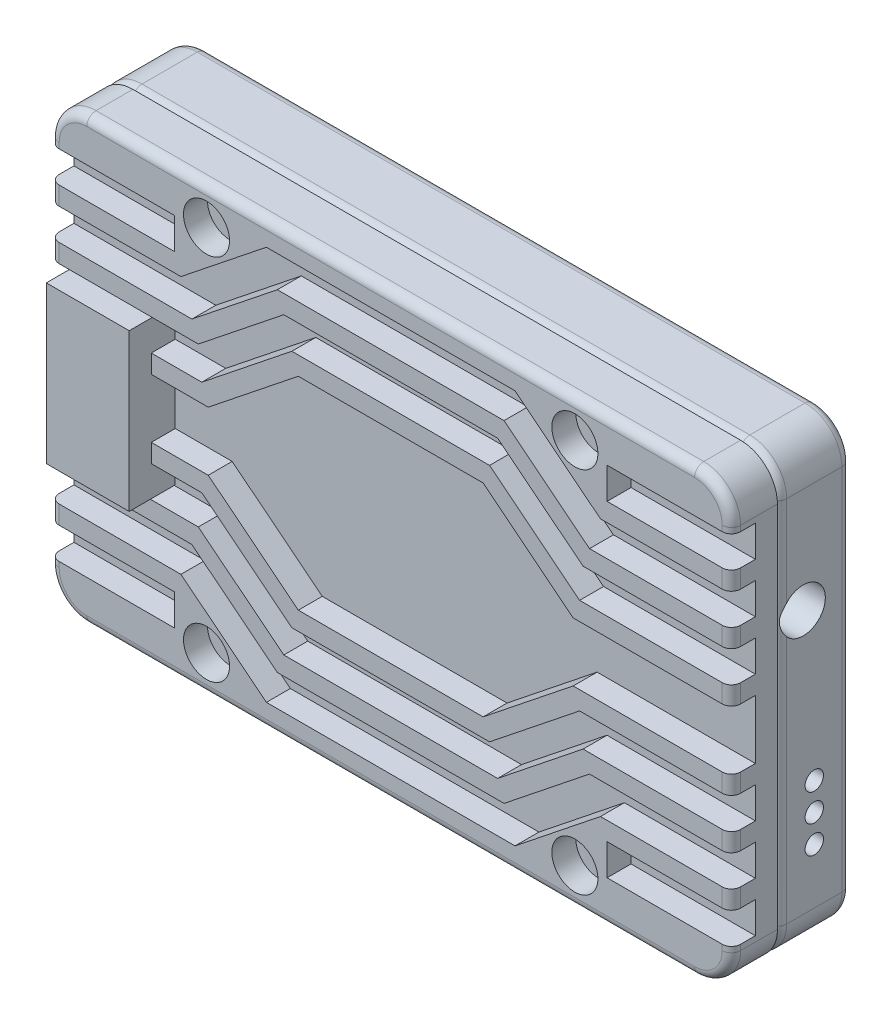
SolidWorks part; units mm, degrees
other "bottom"
other "fin"
other "plug"
ref_plane "Front Plane" through (0, 0, 0) normal (0, 0, 1) x (1, 0, 0)
ref_plane "Top Plane" through (0, 0, 0) normal (0, 1, 0) x (1, 0, 0)
ref_plane "Right Plane" through (0, 0, 0) normal (1, 0, 0) x (0, 0, -1)
sketch "Sketch1" plane through (0, 0, 0) normal (0, 0, 1) x (1, 0, 0)
  line L1 (-16.5, 12) -> (16.5, 12)
  line L2 (-18.5, 10) -> (-18.5, -10)
  line L3 (-16.5, -12) -> (16.5, -12)
  line L4 (18.5, 10) -> (18.5, -10)
  line L5 (-18.5, 12) -> (18.5, -12) construction
  line L6 (-18.5, -12) -> (18.5, 12) construction
  arc A0 (-18.5, -10) -> (-16.5, -12) centre (-16.5, -10) ccw
  arc A1 (16.5, -12) -> (18.5, -10) centre (16.5, -10) ccw
  arc A2 (16.5, 12) -> (18.5, 10) centre (16.5, 10) cw
  arc A3 (-16.5, 12) -> (-18.5, 10) centre (-16.5, 10) ccw
  point P0 (0, 0)
  dimension "D3" = 2
  dimension "D1" = 37
  dimension "D2" = 24
extrude "Boss-Extrude1" add sketch "Sketch1" along normal blind 4
fillet "Fillet1" radius 0.5 16 edges at (0, -12, 0) (17.9142, -11.4142, 0) (18.5, 0, 0) (17.9142, 11.4142, 0) (0, 12, 0) (-17.9142, 11.4142, 0) (-18.5, 0, 0) (-17.9142, -11.4142, 0) (-18.5, 0, 4) (-17.9142, 11.4142, 4) (0, 12, 4) (17.9142, 11.4142, 4) (18.5, 0, 4) (17.9142, -11.4142, 4) (0, -12, 4) (-17.9142, -11.4142, 4)
sketch "Sketch3" plane through (0, -12, 0) normal (0, -1, 0) x (1, 0, 0)
  line L0 (18.5, 3.5) -> (18.5, 0.5) construction
  line L1 (-18.5, 3.5) -> (-18.5, 0.5) construction
  line L2 (16.5, 0) -> (-16.5, 0) construction
  circle A0 centre (-10, 2) radius 1.2
  circle A1 centre (10, 2) radius 1.2
  dimension "D4" = 2.4
  dimension "D1" = 8.5
  dimension "D2" = 8.5
  dimension "D3" = 2
extrude "Boss-Extrude3" add sketch "Sketch3" along normal blind 1.4
sketch "Sketch8" plane through (18.5, 0, 0) normal (1, 0, 0) x (0, 0, -1)
  line L0 (0, 10) -> (0, -10) construction
  line L1 (-2, -4) -> (-2, -7) construction
  line L2 (-3.5, -12) -> (-0.5, -12) construction
  line L3 (-3.5, 12) -> (-0.5, 12) construction
  circle A0 centre (-2.6, 4.3) radius 1.2
  circle A1 centre (-2, -4) radius 0.5
  circle A2 centre (-2, -5.5) radius 0.5
  circle A3 centre (-2, -7) radius 0.5
  point P13 (-2, -5.5)
  dimension "D1" = 2.4
  dimension "D3" = 1
  dimension "D2" = 2.6
  dimension "D4" = 3
  dimension "D5" = 5
  dimension "D6" = 2
  dimension "D7" = 7.7
extrude "Cut-Extrude3" cut sketch "Sketch8" against normal blind 2
sketch "Sketch2" plane through (0, 0, 4) normal (0, 0, 1) x (1, 0, 0)
  line L4 (-18.5, 10) -> (-18.5, -10)
  line L5 (-16.5, -12) -> (16.5, -12)
  line L6 (18.5, -10) -> (18.5, 10)
  line L7 (16.5, 12) -> (-16.5, 12)
  line L8 (-18.5, 10) -> (-18.5, -10)
  line L9 (-16.5, -12) -> (16.5, -12)
  line L10 (18.5, -10) -> (18.5, 10)
  line L11 (16.5, 12) -> (-16.5, 12)
  arc A4 (-18.5, -10) -> (-16.5, -12) centre (-16.5, -10) ccw
  arc A5 (16.5, -12) -> (18.5, -10) centre (16.5, -10) ccw
  arc A6 (18.5, 10) -> (16.5, 12) centre (16.5, 10) ccw
  arc A7 (-16.5, 12) -> (-18.5, 10) centre (-16.5, 10) ccw
  arc A8 (-18.5, -10) -> (-16.5, -12) centre (-16.5, -10) ccw
  arc A9 (16.5, -12) -> (18.5, -10) centre (16.5, -10) ccw
  arc A10 (18.5, 10) -> (16.5, 12) centre (16.5, 10) ccw
  arc A11 (-16.5, 12) -> (-18.5, 10) centre (-16.5, 10) ccw
  dimension "D1" = 0
extrude "Boss-Extrude2" add sketch "Sketch2" along normal blind 2.5 separate body
fillet "Fillet2" radius 0.5 8 edges at (0, 12, 6.5) (17.9142, 11.4142, 6.5) (18.5, 0, 6.5) (17.9142, -11.4142, 6.5) (0, -12, 6.5) (-17.9142, -11.4142, 6.5) (-18.5, 0, 6.5) (-17.9142, 11.4142, 6.5)
sketch "Sketch6" plane through (0, 0, 6.5) normal (0, 0, 1) x (1, 0, 0)
  line L0 (0, 0) -> (50000, 0) construction
  line L1 (0, 0) -> (0, -50000) construction
  line L2 (0, 10.7) -> (6.75, 10.7)
  line L3 (6.75, 10.7) -> (11.39, 7)
  line L4 (11.39, 7) -> (18.5, 7)
  line L5 (18.5, 10) -> (18.5, -10) construction
  line L6 (18.5, 7) -> (18.5, 5.3)
  line L7 (18.5, 5.3) -> (10.7952, 5.3)
  line L8 (10.7952, 5.3) -> (6.1552, 9)
  line L9 (6.1552, 9) -> (0, 9)
  line L10 (0, 6.5) -> (5.367, 6.5)
  line L11 (5.367, 6.5) -> (10.2578, 2.6)
  line L12 (10.2578, 2.6) -> (18.5, 2.6)
  line L13 (18.5, 2.6) -> (18.5, 4.3)
  line L14 (18.5, 4.3) -> (10.4453, 4.3)
  line L15 (10.4453, 4.3) -> (5.8053, 8)
  line L16 (5.8053, 8) -> (0, 8)
  line L17 (0, 5.5) -> (5.0171, 5.5)
  line L18 (5.0171, 5.5) -> (9.9079, 1.6)
  line L19 (9.9079, 1.6) -> (18.5, 1.6)
  line L20 (18.5, 1.6) -> (18.5, 0)
  line L21 (-16.5, 12) -> (16.5, 12) construction
  line L22 (0, 5.5) -> (0, 0)
  line L23 (0, 0) -> (18.5, 0)
  line L24 (0, 10.7) -> (0, 9)
  line L25 (0, 8) -> (0, 6.5)
  line L27 (18.5, 9.7) -> (11.75, 9.7)
  line L28 (18.5, 9.7) -> (18.5, 8)
  line L29 (18.5, 8) -> (11.75, 8)
  line L30 (11.75, 9.7) -> (11.75, 8)
  circle A0 centre (10, 10) radius 1.25
  dimension "D19" = 2.5
  dimension "D1" = 1.6
  dimension "D2" = 1.7
  dimension "D3" = 1.7
  dimension "D4" = 1
  dimension "D5" = 1
  dimension "D6" = 1.3
  dimension "D7" = 1.7
  dimension "D8" = 1
  dimension "D9" = 1
  dimension "D10" = 5.5
  dimension "D11" = 1.7
  dimension "D12" = 1
  dimension "D13" = 1.446
  dimension "D14" = 1
  dimension "D15" = 11.75
  dimension "D16" = 7.11
  dimension "D17" = 10
  dimension "D18" = 10
  dimension "D20" = 1.7
  dimension "D21" = 6.75
  dimension "D22" = 1
extrude "Cut-Extrude2" cut sketch "Sketch6" against normal blind 1.3
mirror "Mirror3" about plane through (0, 0, 0) normal (1, 0, 0) of "Cut-Extrude2" second plane through (0, 0, 0) second plane normal (0, 1, 0)
sketch "Sketch4" plane through (0, 0, 6.5) normal (0, 0, 1) x (1, 0, 0)
  line L0 (-18.5, -10) -> (-18.5, -9.7) construction
  line L1 (-13, -4.25) -> (-18.5, -4.25)
  line L2 (-13, -4.25) -> (-13, 4.25)
  line L3 (-13, 4.25) -> (-18.5, 4.25)
  line L4 (-18.5, -4.25) -> (-18.5, 4.25)
  point P6 (-13, 0)
  dimension "D1" = 5.5
  dimension "D2" = 8.5
extrude "Cut-Extrude1" cut sketch "Sketch4" against normal up to vertex
sketch "Sketch5" plane through (-13, 0, 0) normal (-1, 0, 0) x (0, 0, 1)
  line L0 (4, -4.25) -> (5.2, -4.25) construction
  line L1 (7.7, 4.25) -> (5, 4.25)
  line L2 (7.7, 4.25) -> (7.7, -4.25)
  line L3 (7.7, -4.25) -> (5, -4.25)
  line L4 (5, 4.25) -> (5, 3.75)
  line L6 (5, -3.75) -> (4, -3.75)
  line L8 (5, 3.75) -> (4, 3.75)
  line L9 (4, -3.75) -> (4, 3.75)
  line L10 (4, 4.25) -> (5.2, 4.25) construction
  line L11 (4, -4.25) -> (5.2, -4.25) construction
  line L12 (5, -3.75) -> (5, -4.25)
  line L13 (7.4, 3.95) -> (5.3, 3.95)
  line L14 (5.3, 3.95) -> (5.3, 3.45)
  line L15 (5.3, 3.45) -> (4.3, 3.45)
  line L16 (4.3, -3.45) -> (4.3, 3.45)
  line L17 (5.3, -3.45) -> (4.3, -3.45)
  line L18 (5.3, -3.45) -> (5.3, -3.95)
  line L19 (7.4, -3.95) -> (5.3, -3.95)
  line L20 (7.4, 3.95) -> (7.4, -3.95)
  line L21 (4, -4.25) -> (4, 4.25) construction
  dimension "D1" = 1
  dimension "D2" = 3.7
  dimension "D3" = 0.5
  dimension "D4" = 0.5
  dimension "D5" = 0.3
extrude "Boss-Extrude4" add sketch "Sketch5" along normal blind 4.5 separate body
sketch "Sketch7" plane through (-13, 0, 0) normal (1, 0, 0) x (0, 0, -1)
  line L1 (-7.7, 4.25) -> (-4, 4.25)
  line L2 (-7.7, 4.25) -> (-7.7, -4.25)
  line L3 (-7.7, -4.25) -> (-4, -4.25)
  line L4 (-4, 4.25) -> (-4, -4.25)
extrude "Boss-Extrude5" add sketch "Sketch7" against normal blind 2
